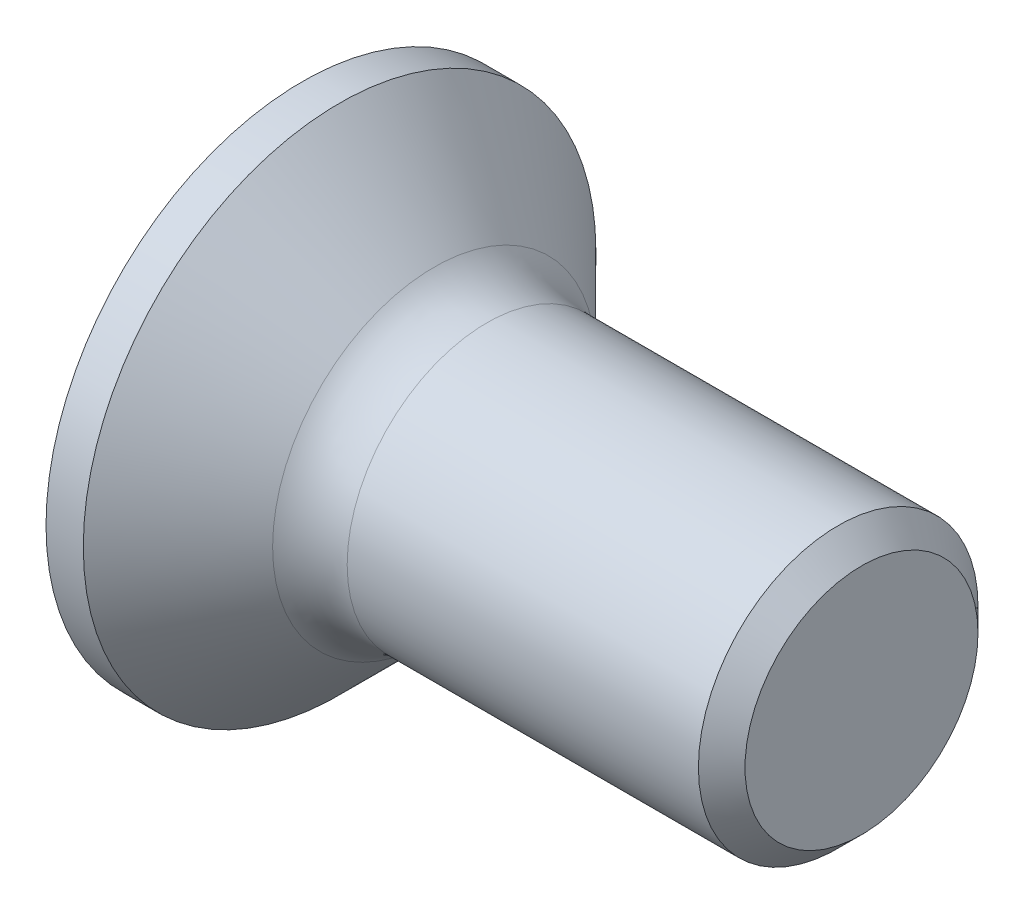
SolidWorks part; units mm, degrees
material "AISI 1045 Aço, trefilado"
ref_plane "Plane1" through (0, 0, 0) normal (0, 0, 1) x (1, 0, 0)
ref_plane "Plane2" through (0, 0, 0) normal (0, 1, 0) x (1, 0, 0)
ref_plane "Plane3" through (0, 0, 0) normal (1, 0, 0) x (0, 0, -1)
sketch "BodySke" plane through (0, 0, 0) normal (0, 0, 1) x (1, 0, 0)
  line L0 (0, 0) -> (0, 2.75)
  line L1 (0, 2.75) -> (0.4, 2.75)
  line L2 (1.65, 1.5) -> (6, 1.5)
  line L3 (6, 1.5) -> (6, 0)
  line L4 (6, 0) -> (0, 0)
  line L5 (-6.35, 0) -> (82.55, 0) construction
  line L6 (1.65, -1.5) -> (6, -1.5) construction
  line L7 (0.4, -2.75) -> (1.65, -1.5) construction
  line L8 (0.4, 2.75) -> (1.65, 1.5)
  line L9 (0, -2.75) -> (0.4, -2.75) construction
  line L10 (2.15, 3.0875) -> (2.15, -6.4375) construction
  line L11 (0, 6.35) -> (0, -3.175) construction
  dimension "Diameter" = 3
  dimension "Length" = 6
  dimension "Head_ht" = 1.65
  dimension "Head_dia" = 5.5
  dimension "Head_ang" = 90
  dimension "D6" = 0.4
  dimension "Advance" = 0.5
  dimension "Thread_nom" = 6
revolve "Base-Revolve" add sketch "BodySke"
cosmetic thread "ThreadCosmetic" [suppressed]
fillet "Fillet1" radius 0.8 1 edges at (1.65, 0, 1.5)
sketch "Sketch3" plane through (0, 0, 0) normal (-1, 0, 0) x (0, 0, 1)
  line L0 (-0.37, 1.5) -> (0.37, 1.5)
  line L1 (0.37, 1.5) -> (0.37, -1.5)
  line L2 (0.37, -1.5) -> (-0.37, -1.5)
  line L3 (-0.37, -1.5) -> (-0.37, 1.5)
  dimension "D1" = 1.5
  dimension "Cross_dia" = 3
  dimension "D2" = 0.37
  dimension "Cross_width" = 0.74
ref_plane "Plane4" through (2.01, 0, 0) normal (-1, 0, 0) x (0, 0, 1)
sketch "Sketch4" plane through (2.01, 0, 0) normal (-1, 0, 0) x (0, 0, 1)
  line L0 (-0.37, 0.4979) -> (0.37, 0.4979)
  line L3 (0.37, 0.4979) -> (0.37, -0.4979)
  line L4 (0.37, -0.4979) -> (-0.37, -0.4979)
  line L5 (-0.37, -0.4979) -> (-0.37, 0.4979)
  dimension "D1" = 0.74
  dimension "D2" = 0.9957
  dimension "D3" = 0.37
  dimension "D4" = 0.4979
loft "Recess" cut profiles "Sketch3", "Sketch4"
pattern_circular "RecPat" count 2 every 90 about axis through (0, 0, 0) along (1, 0, 0) of "Recess"
sketch "RecCorSke" plane through (0, 0, 0) normal (0, 0, 1) x (1, 0, 0)
  line L0 (-3.175, 0) -> (15.875, 0) construction
  line L2 (0, 0) -> (0, 0.6966)
  line L3 (0, 0.6966) -> (2.01, 0.556)
  line L4 (2.01, 0.556) -> (2.1907, 0)
  line L5 (2.1907, 0) -> (0, 0)
  dimension "Diameter" = 1.112
  dimension "Depth" = 2.01
  dimension "Draft_angle" = 4
  dimension "Bottom_angle" = 18
revolve "RecessCore" cut sketch "RecCorSke" angle 360 about L0
sketch "ThdSchSke" plane through (0, 0, 0) normal (0, 0, 1) x (1, 0, 0)
  line L0 (2.15, -1.2195) -> (1.9536, -1.5)
  line L1 (2.15, -1.2195) -> (2.3464, -1.5)
  line L2 (2.3464, -1.5) -> (2.3464, -1.875)
  line L3 (-3.175, 0) -> (5.1513, 0) construction
  line L5 (2.3464, -1.875) -> (1.9536, -1.875)
  line L6 (1.9536, -1.875) -> (1.9536, -1.5)
  line L7 (0, 2.75) -> (0, -2.75) construction
  dimension "Thread_minor" = 2.439
  dimension "Diameter" = 3
  dimension "Start" = 2.15
  dimension "SideAngle" = 55
  dimension "VeeAngle" = 70
  dimension "Overcut" = 3.75
revolve "ThreadSchematic" [suppressed] cut sketch "ThdSchSke" angle 360 about L3
pattern_linear "ThdSchPat" [suppressed]
chamfer "Chanfro1" distance 0.25 angle 45 1 edges at (6, 0, 1.5)
equation "\"D1@Sketch3\" = \"Cross_dia@Sketch3\" / 2"
equation "\"D2@Sketch3\" = \"Cross_width@Sketch3\" / 2"
equation "\"Depth@RecCorSke\" = \"Cross_depth@Plane4\""
equation "\"D1@Sketch4\" = \"Cross_width@Sketch3\""
equation "\"D2@Sketch4\" = \"Cross_dia@Sketch3\" - 2.0 * \"Cross_depth@Plane4\" * tan(26.5  * 0.017453292)"
equation "\"D3@Sketch4\" = \"D1@Sketch4\" / 2"
equation "\"D4@Sketch4\" = \"D2@Sketch4\" / 2"
equation "\"Thread_length@ThreadCosmetic\" = ((sgn( (\"Length@BodySke\" - \"Advance@BodySke\" * 1.0 - \"Head_ht@BodySke\" ) - \"Thread_nom@BodySke\" )-1)*( (\"Length@BodySke\" - \"Advance@BodySke\" * 1.0 - \"Head_ht@BodySke\" ) - \"Thread_nom@BodySke\" ))/-2+ \"Thread_nom@BodySke\""
equation "\"Thread_minor@ThdSchSke\" = \"Thread_minor@ThreadCosmetic\""
equation "\"Diameter@ThdSchSke\" = \"Diameter@BodySke\""
equation "\"Overcut@ThdSchSke\" = \"Diameter@BodySke\" * 1.25"
equation "\"Start@ThdSchSke\" = 0.000001 + \"Length@BodySke\" - \"Thread_length@ThreadCosmetic\"  '---Countersunk---"
equation "\"Num_threads@ThdSchPat\" = int( \"Thread_length@ThreadCosmetic\" / \"Advance@BodySke\" + 0.999 )  + 1"
equation "\"Advance@ThdSchPat\" = \"Thread_length@ThreadCosmetic\" /  (\"Num_threads@ThdSchPat\" - 1) 'relax it"
